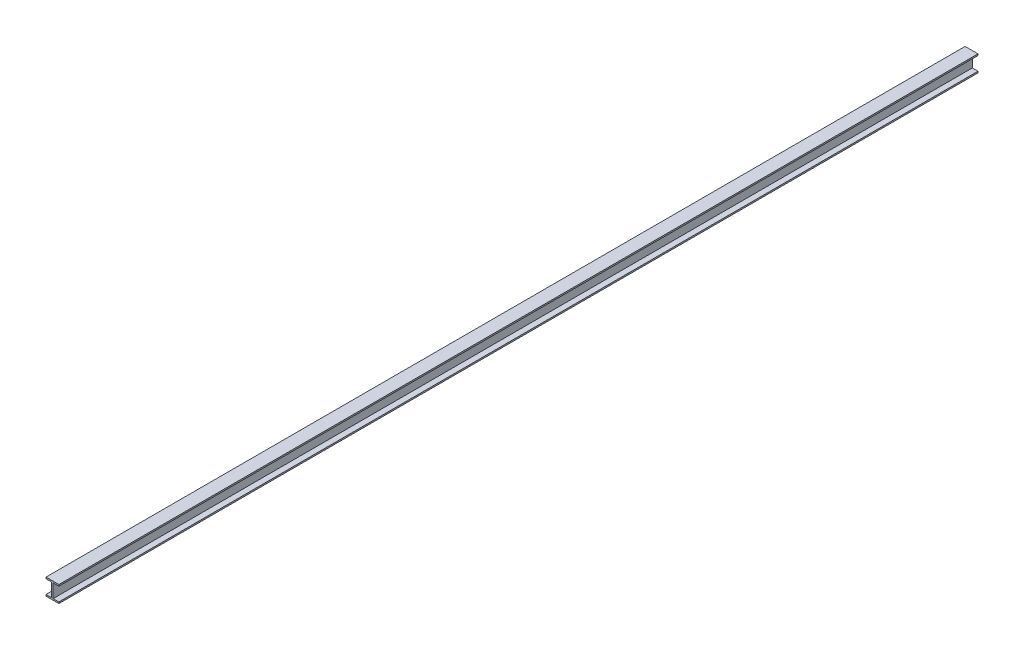
SolidWorks part; units mm, degrees
ref_plane "Front Plane" through (0, 0, 0) normal (0, 0, 1) x (1, 0, 0)
ref_plane "Top Plane" through (0, 0, 0) normal (0, 1, 0) x (1, 0, 0)
ref_plane "Right Plane" through (0, 0, 0) normal (1, 0, 0) x (0, 0, -1)
sketch "Sketch1" plane through (0, 0, 0) normal (0, 0, 1) x (1, 0, 0)
  line L0 (156, -32) -> (280, -32)
  line L1 (0, 0) -> (280, 0)
  line L2 (0, 0) -> (0, -32)
  line L3 (0, -360) -> (280, -360)
  line L4 (280, 0) -> (280, -32)
  line L5 (124, 0) -> (156, 0)
  line L6 (124, -32) -> (124, -328)
  line L7 (124, -360) -> (156, -360)
  line L8 (156, -32) -> (156, -328)
  line L9 (0, 0) -> (280, 0)
  line L10 (0, 0) -> (0, -32)
  line L11 (0, -32) -> (124, -32)
  line L12 (280, 0) -> (280, -32)
  line L13 (0, -360) -> (280, -360)
  line L14 (0, -360) -> (0, -328)
  line L15 (0, -328) -> (124, -328)
  line L16 (280, -360) -> (280, -328)
  line L17 (0, -328) -> (0, -360)
  line L18 (280, -328) -> (280, -360)
  line L19 (156, -328) -> (280, -328)
  dimension "D1" = 280
  dimension "D2" = 360
  dimension "D3" = 32
  dimension "D4" = 32
  dimension "D5" = 124
  dimension "D6" = 124
extrude "Boss-Extrude1" add sketch "Sketch1" along normal blind 20000 contours L19 L8 L0 L4 L1 L2 L11 L6 L15 L14 L3 L16
